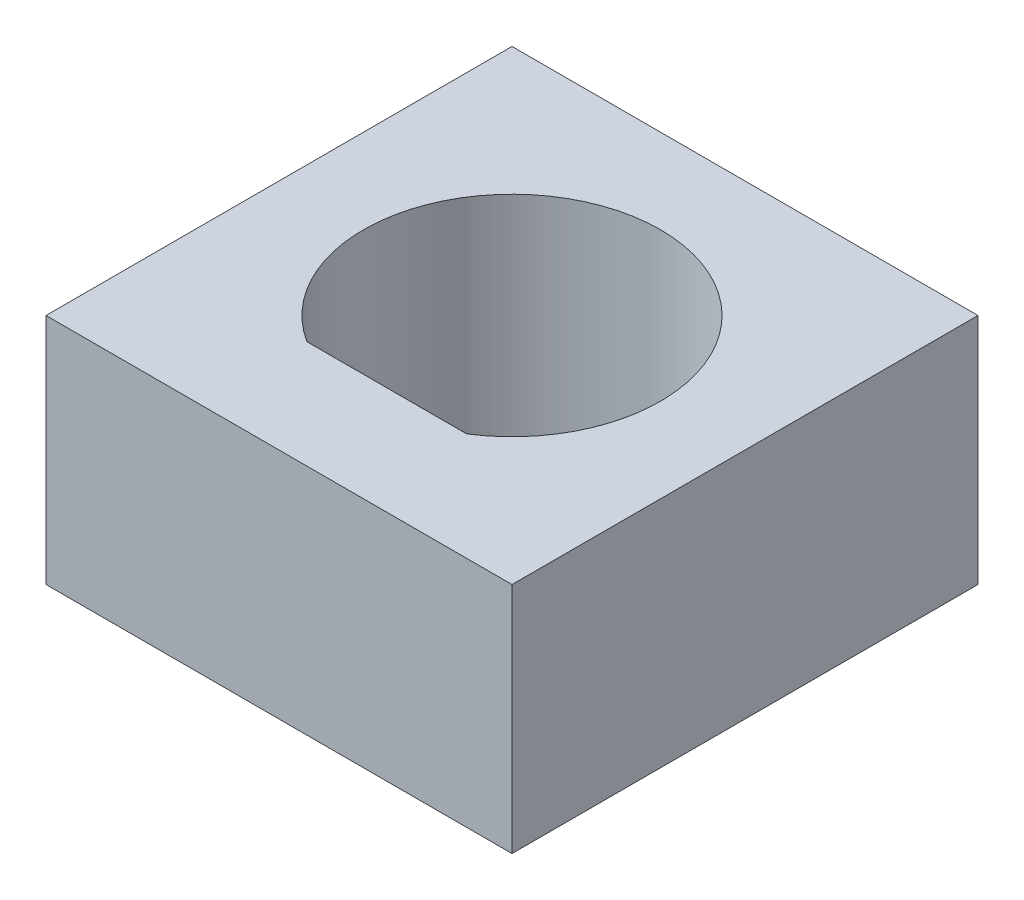
SolidWorks part; units mm, degrees
ref_plane "Front Plane" through (0, 0, 0) normal (0, 0, 1) x (1, 0, 0)
ref_plane "Top Plane" through (0, 0, 0) normal (0, 1, 0) x (1, 0, 0)
ref_plane "Right Plane" through (0, 0, 0) normal (1, 0, 0) x (0, 0, -1)
sketch "Sketch1" plane through (0, 0, 0) normal (0, 1, 0) x (1, 0, 0)
  line L0 (0, 0) -> (0, -3.2385) construction
  line L1 (0, 0) -> (3.2385, 0) construction
  line L2 (0, -2.7305) -> (1.7413, -2.7305) construction
  line L3 (1.7413, -2.7305) -> (-1.7413, -2.7305)
  line L5 (5.08, -5.08) -> (-5.08, -5.08)
  line L6 (5.08, -5.08) -> (5.08, 5.08)
  line L7 (5.08, 5.08) -> (-5.08, 5.08)
  line L8 (-5.08, -5.08) -> (-5.08, 5.08)
  line L9 (5.08, -5.08) -> (-5.08, 5.08) construction
  line L10 (5.08, 5.08) -> (-5.08, -5.08) construction
  circle A0 centre (0, 0) radius 3.2385 construction
  arc A1 (1.7413, -2.7305) -> (-1.7413, -2.7305) centre (0, 0) ccw
  dimension "D1" = 6.477
  dimension "D2" = 0.508
  dimension "D3" = 10.16
  dimension "D4" = 10.16
extrude "Boss-Extrude1" add sketch "Sketch1" along normal blind 5.08
